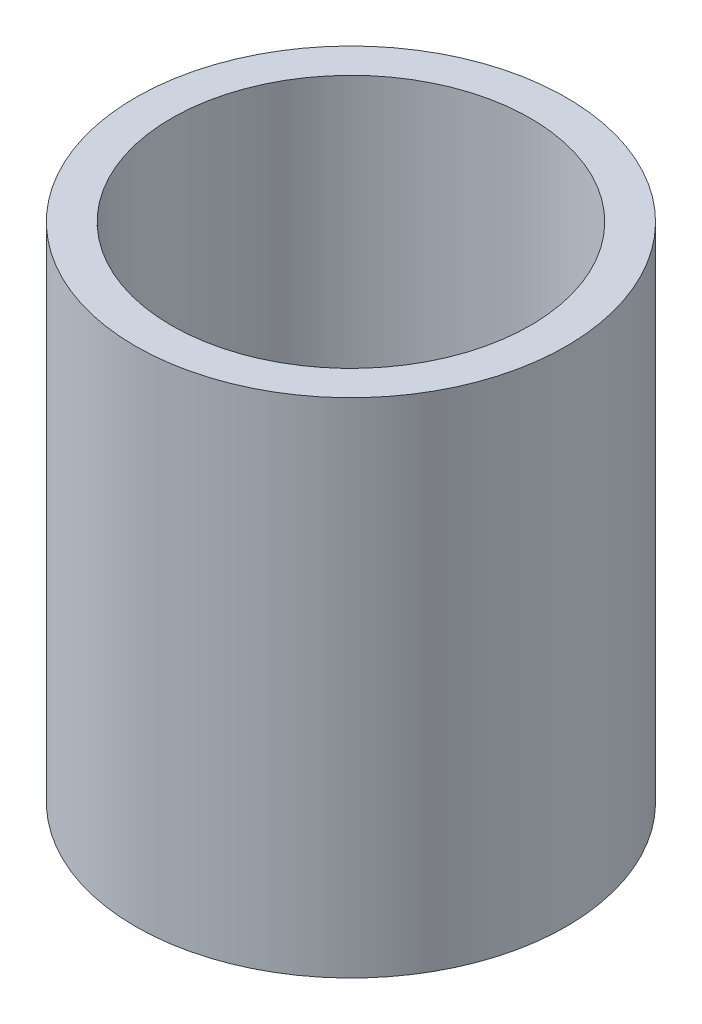
SolidWorks part; units mm, degrees
ref_plane "Front" through (0, 0, 0) normal (0, 0, 1) x (1, 0, 0)
ref_plane "Top" through (0, 0, 0) normal (0, 1, 0) x (1, 0, 0)
ref_plane "Right" through (0, 0, 0) normal (1, 0, 0) x (0, 0, -1)
sketch "Sketch1" plane through (0, 0, 0) normal (0, 1, 0) x (1, 0, 0)
  circle A0 centre (0, 0) radius 2.5
  circle A1 centre (0, 0) radius 3
extrude "Boss-Extrude1" add sketch "Sketch1" along normal blind 7
